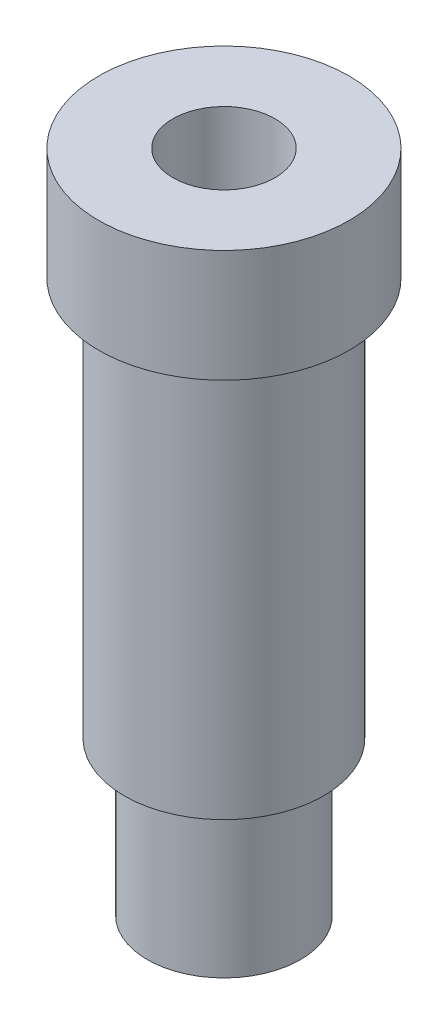
SolidWorks part; units mm, degrees
ref_plane "Plan de face" through (0, 0, 0) normal (0, 0, 1) x (1, 0, 0)
ref_plane "Plan de dessus" through (0, 0, 0) normal (0, 1, 0) x (1, 0, 0)
ref_plane "Plan de droite" through (0, 0, 0) normal (1, 0, 0) x (0, 0, -1)
sketch "Esquisse1" plane through (0, 0, 0) normal (0, 0, 1) x (1, 0, 0)
  line L0 (0, -2.8217) -> (0, 16.3072) construction
  line L1 (-0.441, 0) -> (4.3372, 0) construction
  line L2 (1.5, -0.5737) -> (1.5, 3.7139) construction
  line L3 (1.95, 2.4145) -> (1.95, 11.6547) construction
  line L4 (2.45, 9.8396) -> (2.45, 13.6553) construction
  line L5 (-0.3064, 13) -> (4.3372, 13) construction
  line L6 (3.2853, 10.8) -> (0.2809, 10.8) construction
  line L7 (3.2853, 3) -> (0.1381, 3) construction
  line L8 (0, 13) -> (2.45, 13)
  line L9 (2.45, 13) -> (2.45, 10.8)
  line L10 (2.45, 10.8) -> (1.95, 10.8)
  line L11 (1.95, 10.8) -> (1.95, 3)
  line L12 (1.95, 3) -> (1.5, 3)
  line L13 (1.5, 3) -> (1.5, 0)
  line L14 (1.5, 0) -> (0, 0)
  line L15 (0, 0) -> (0, 13)
  dimension "D1" = 13
  dimension "D2" = 2.2
  dimension "D3" = 3
  dimension "D4" = 2.45
  dimension "D5" = 1.95
  dimension "D6" = 1.5
revolve "Révolution2" add sketch "Esquisse1" angle 360 about L0
sketch "Esquisse2" plane through (0, 13, 0) normal (0, 1, 0) x (-1, 0, 0)
  circle A0 centre (0, 0) radius 1
extrude "Enlèv. mat.-Extru.1" cut sketch "Esquisse2" against normal through all
